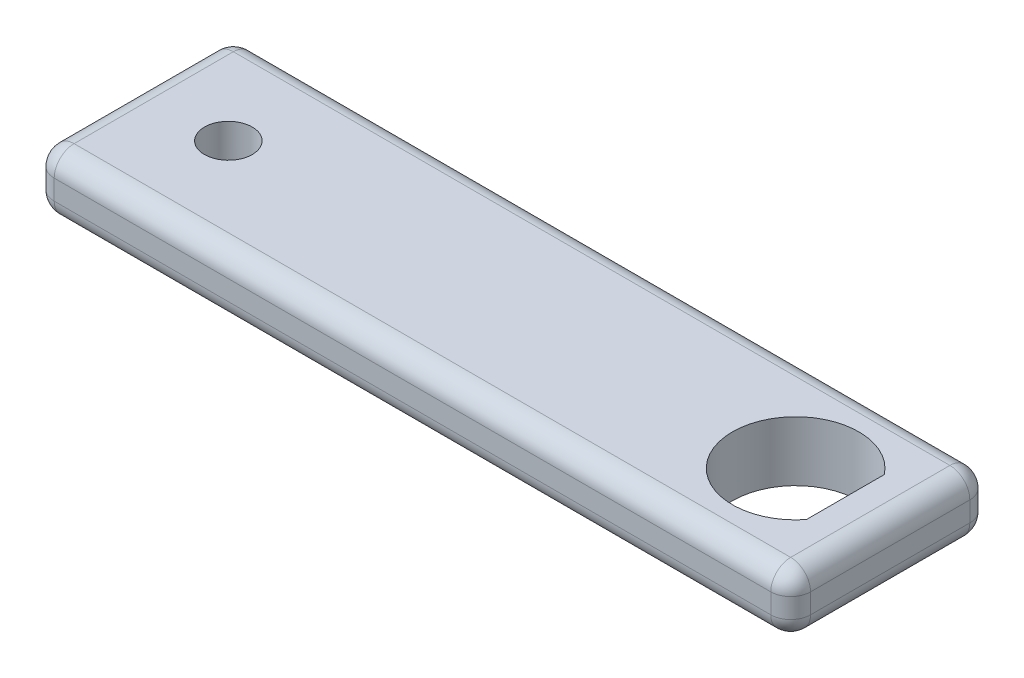
SolidWorks part; units mm, degrees
ref_plane "Front Plane" through (0, 0, 0) normal (0, 0, 1) x (1, 0, 0)
ref_plane "Top Plane" through (0, 0, 0) normal (0, 1, 0) x (1, 0, 0)
ref_plane "Right Plane" through (0, 0, 0) normal (1, 0, 0) x (0, 0, -1)
sketch "Sketch1" plane through (0, 0, 0) normal (0, 1, 0) x (1, 0, 0)
  line L1 (0, 0) -> (76, 0)
  line L2 (0, 0) -> (0, 20)
  line L3 (0, 20) -> (76, 20)
  line L4 (76, 0) -> (76, 20)
  dimension "D1" = 20
  dimension "D2" = 76
extrude "Boss-Extrude1" add sketch "Sketch1" along normal blind 6
sketch "Sketch2" plane through (0, 6, 0) normal (0, 1, 0) x (1, 0, 0)
  line L0 (76, 20) -> (0, 20) construction
  line L1 (0, 20) -> (0, 0) construction
  line L2 (76, 0) -> (76, 20) construction
  line L3 (0, 0) -> (76, 0) construction
  line L4 (71.5, 13.9144) -> (71.5, 6.0856)
  circle A0 centre (9.5, 10) radius 2.4
  arc A1 (71.5, 13.9144) -> (71.5, 6.0856) centre (66.5, 10) ccw
  dimension "D1" = 4.8
  dimension "D5" = 6.35
  dimension "D2" = 10
  dimension "D3" = 9.5
  dimension "D4" = 9.5
  dimension "D6" = 10
  dimension "D7" = 5
extrude "Cut-Extrude1" cut sketch "Sketch2" against normal up to surface (6 mm away) up to face at (38, 0, -10)
fillet "Fillet1" radius 2 12 edges at (0, 3, -20) (0, 3, 0) (76, 3, -20) (76, 3, 0) (0, 0, -10) (38, 0, -20) (76, 0, -10) (38, 0, 0) (0, 6, -10) (38, 6, 0) (76, 6, -10) (38, 6, -20)
